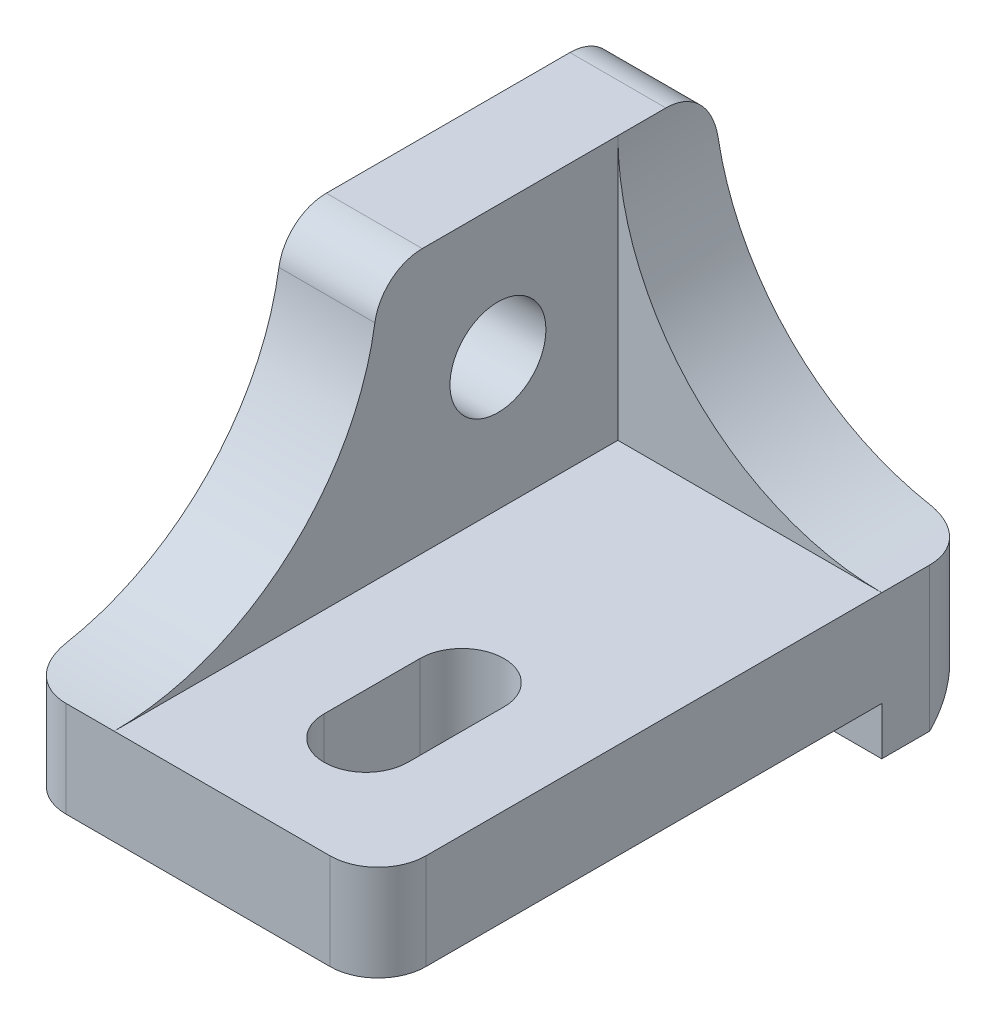
SolidWorks part; units mm, degrees
other "Marcação1"
sketch "Esboço9" plane through (0, 15, 25) normal (0.4812, 0.87, 0.1078) x (-0.8404, 0.4928, -0.2257)
material "PVC Rígido"
ref_plane "Plano frontal" through (0, 0, 0) normal (0, 0, 1) x (1, 0, 0)
ref_plane "Plano superior" through (0, 0, 0) normal (0, 1, 0) x (1, 0, 0)
ref_plane "Plano direito" through (0, 0, 0) normal (1, 0, 0) x (0, 0, -1)
sketch "Esboço1" plane through (0, 0, 0) normal (0, 0, 1) x (1, 0, 0)
  line L0 (0, 0) -> (-15, 0)
  line L1 (-15, 0) -> (-15, 15)
  line L2 (-15, 15) -> (-11, 15)
  line L3 (-11, 15) -> (-11, 4)
  line L4 (-11, 4) -> (0, 4)
  line L5 (0, 4) -> (0, 0)
extrude "Ressalto-extrusão1" add sketch "Esboço1" along normal blind 25
sketch "Esboço2" plane through (0, 0, 0) normal (0, 0, -1) x (-1, 0, 0)
  line L1 (0, 4) -> (11, 4)
  line L4 (11, 4) -> (11, 15)
  arc A0 (11, 15) -> (0, 4) centre (0, 15) cw
extrude "Ressalto-extrusão2" add sketch "Esboço2" against normal blind 4
sketch "Esboço3" plane through (0, 0, 0) normal (1, 0, 0) x (0, 0, -1)
  line L0 (0, 0) -> (-4, 0)
  line L1 (-25, 0) -> (0, 0) construction
  line L2 (-4, 0) -> (-4, -2)
  line L5 (-4, -2) -> (-2, -2)
  line L6 (-2, -2) -> (0, 0)
extrude "Ressalto-extrusão4" add sketch "Esboço3" against normal blind 4
pattern_linear "Padrão linear1" count 2 spacing 11 along (-1, 0, 0) of "Ressalto-extrusão4"
sketch "Esboço5" plane through (0, 4, 0) normal (0, 1, 0) x (1, 0, 0)
  line L0 (-5.5, -20) -> (-5.5, -16) construction
  line L1 (0, -4) -> (-11, -4) construction
  line L2 (-7.25, -20) -> (-7.25, -16)
  line L3 (-3.75, -20) -> (-3.75, -16)
  line L5 (0, -25) -> (0, -4) construction
  arc A0 (-7.25, -20) -> (-3.75, -20) centre (-5.5, -20) ccw
  arc A1 (-3.75, -16) -> (-7.25, -16) centre (-5.5, -16) ccw
  point P4 (-5.5, -18)
  dimension "D1" = 16
  dimension "D2" = 5.5
extrude "Corte-extrusão1" cut sketch "Esboço5" against normal through all
sketch "Esboço6" plane through (-11, 0, 0) normal (1, 0, 0) x (0, 0, -1)
  line L0 (-25, 4) -> (-4, 4) construction
  circle A0 centre (-9, 9.5) radius 2
  dimension "D1" = 9
  dimension "D2" = 5.5
extrude "Corte-extrusão2" cut sketch "Esboço6" against normal through all
sketch "Esboço8" plane through (-11, 0, 0) normal (1, 0, 0) x (0, 0, -1)
  line L2 (-25, 4) -> (-25, 15)
  line L3 (-25, 15) -> (-14, 15)
  arc A0 (-14, 15) -> (-25, 4) centre (-25, 15) cw
extrude "Corte-extrusão3" cut sketch "Esboço8" against normal through all
fillet "Filete2" radius 2 1 edges at (-13, 15, 14)
fillet "Filete3" radius 2 1 edges at (0, 2, 25)
fillet "Filete4" radius 2 1 edges at (-15, 2, 25)
fillet "Filete5" radius 2 1 edges at (0, 2, 0)
fillet "Filete6" radius 2 1 edges at (-13, 15, 0)
